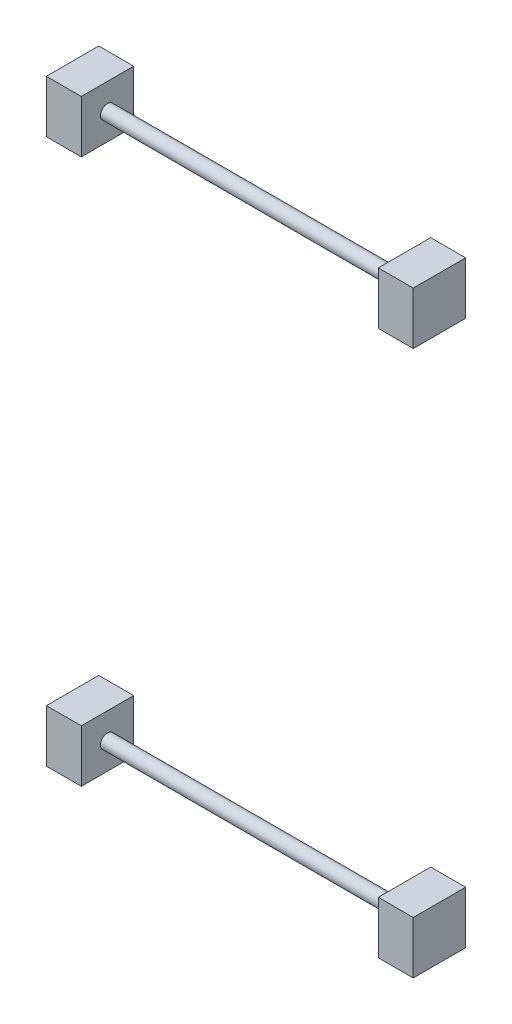
SolidWorks part; units mm, degrees
ref_plane "Front Plane" through (0, 0, 0) normal (0, 0, 1) x (1, 0, 0)
ref_plane "Top Plane" through (0, 0, 0) normal (0, 1, 0) x (1, 0, 0)
ref_plane "Right Plane" through (0, 0, 0) normal (1, 0, 0) x (0, 0, -1)
sketch "Sketch1" plane through (-23475.5611, 0, 0) normal (-1, 0, 0) x (0, 0, 1)
  line L0 (40617.8588, 5649.6667) -> (40692.8588, 5574.6667) construction
  line L1 (40692.8588, 5574.6667) -> (40617.8588, 5574.6667)
  line L2 (40692.8588, 5574.6667) -> (40692.8588, 5649.6667)
  line L3 (40692.8588, 5649.6667) -> (40617.8588, 5649.6667)
  line L4 (40617.8588, 5574.6667) -> (40617.8588, 5649.6667)
  line L5 (40692.8588, 5649.6667) -> (40617.8588, 5574.6667) construction
  circle A0 centre (40655.3588, 5612.1667) radius 10
  dimension "D1" = 20
  dimension "D2" = 75
extrude "Boss-Extrude1" add sketch "Sketch1" against normal blind 50
pattern_linear "LPattern1" count 2 spacing 475 along (1, 0, 0) of "Boss-Extrude1"
sketch "Sketch2" plane through (-23475.5611, 0, 0) normal (-1, 0, 0) x (0, 0, 1)
  circle A0 centre (40655.3588, 5612.1667) radius 10
  circle A1 centre (40655.3588, 5612.1667) radius 10 construction
extrude "Boss-Extrude2" add sketch "Sketch2" against normal blind 525
pattern_linear "LPattern2" count 2 spacing 780 along (0, 1, 0) of bodies 105
